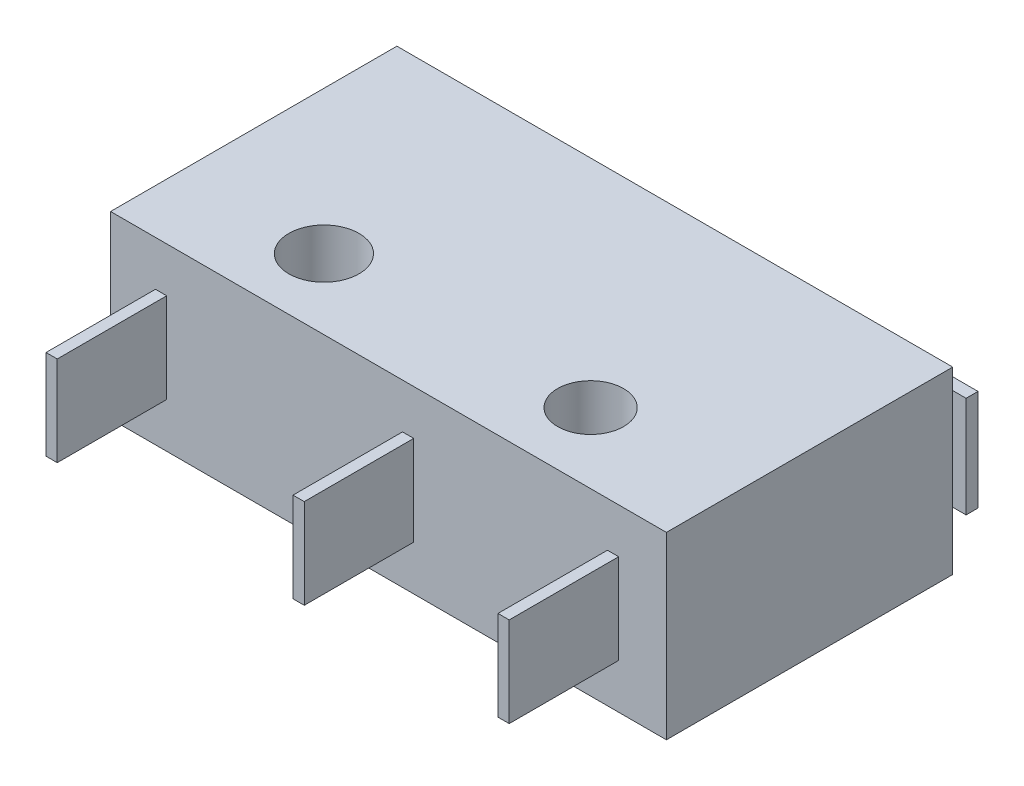
SolidWorks part; units mm, degrees
ref_plane "Front Plane" through (0, 0, 0) normal (0, 0, 1) x (1, 0, 0)
ref_plane "Top Plane" through (0, 0, 0) normal (0, 1, 0) x (1, 0, 0)
ref_plane "Right Plane" through (0, 0, 0) normal (1, 0, 0) x (0, 0, -1)
sketch "Sketch1" plane through (0, 0, 0) normal (0, 1, 0) x (1, 0, 0)
  line L1 (-9.9, -5.1) -> (9.9, -5.1)
  line L2 (-9.9, -5.1) -> (-9.9, 5.1)
  line L3 (-9.9, 5.1) -> (9.9, 5.1)
  line L4 (9.9, -5.1) -> (9.9, 5.1)
  line L5 (0, 5.1) -> (0, -5.1) construction
  line L6 (-9.9, 0) -> (9.9, 0) construction
  point P0 (0, 0)
  dimension "D1" = 10.2
  dimension "D2" = 19.8
extrude "Boss-Extrude1" add sketch "Sketch1" along normal mid plane 6.4
sketch "Sketch2" plane through (0, 0, 0) normal (0, 1, 0) x (1, 0, 0)
  line L0 (-9.9, -2.6) -> (9.9, -2.6) construction
  line L1 (-9.9, 5.1) -> (-9.9, -5.1) construction
  line L2 (9.9, -5.1) -> (9.9, 5.1) construction
  line L3 (-9.9, -5.1) -> (9.9, -5.1) construction
  circle A0 centre (-4.8, -2.6) radius 1.25
  circle A1 centre (4.7, -2.6) radius 1.175
  dimension "D2" = 2.5
  dimension "D3" = 2.35
  dimension "D4" = 9.5
  dimension "D5" = 5.1
  dimension "D1" = 2.5
extrude "Cut-Extrude1" cut sketch "Sketch2" against normal through all both and the other way through all
sketch "Sketch3" plane through (0, 0, 0) normal (0, 1, 0) x (1, 0, 0)
  line L0 (-7.3066, 5.1) -> (-7.3066, 6.2)
  line L1 (9.9, 5.1) -> (-9.9, 5.1) construction
  line L2 (-7.3066, 6.2) -> (9.7, 6.2)
  line L3 (9.7, 6.2) -> (9.7, 5.7756)
  line L4 (9.7, 5.7756) -> (-6.6942, 5.7756)
  line L5 (-6.6942, 5.7756) -> (-6.6942, 5.1)
  line L6 (-6.6942, 5.1) -> (-7.3066, 5.1)
  circle A0 centre (-4.8, -2.6) radius 1.25 construction
  dimension "D1" = 14.5
  dimension "D2" = 8.8
extrude "Boss-Extrude2" add sketch "Sketch3" along normal mid plane 3.6
sketch "Sketch4" plane through (0, 0, 5.1) normal (0, 0, 1) x (1, 0, 0)
  line L0 (-9.9, 3.2) -> (-9.9, -3.2) construction
  line L1 (-8.3, 1.6) -> (-7.9, 1.6)
  line L2 (-8.3, 1.6) -> (-8.3, -1.6)
  line L3 (-8.3, -1.6) -> (-7.9, -1.6)
  line L4 (-7.9, 1.6) -> (-7.9, -1.6)
  line L5 (-8.1, -1.6) -> (-8.1, 1.6) construction
  line L6 (-8.3, 0) -> (-7.9, 0) construction
  point P0 (-8.1, 0)
  dimension "D1" = 3.2
  dimension "D2" = 0.4
  dimension "D3" = 1.6
extrude "Boss-Extrude3" add sketch "Sketch4" along normal blind 3.9
pattern_linear "LPattern1" count 2 spacing 8.8 along (1, 0, 0) of "Boss-Extrude3"
pattern_linear "LPattern2" count 2 spacing 16.1 along (1, 0, 0) of "Boss-Extrude3"
sketch "Sketch5" plane through (0, 0, 0) normal (0, 1, 0) x (1, 0, 0)
  line L0 (9.9, 5.1) -> (-9.9, 5.1) construction
  circle A0 centre (-3.3074, 5.1) radius 0.5071
extrude "Boss-Extrude4" add sketch "Sketch5" along normal mid plane 3.4
